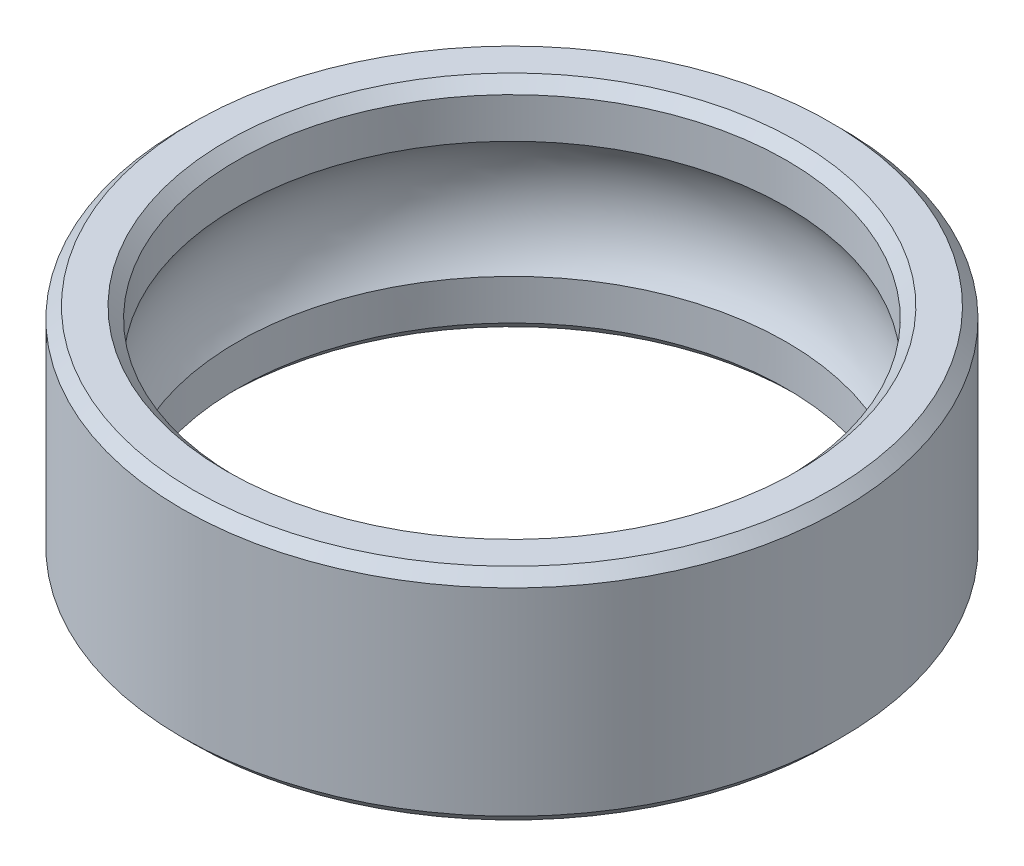
SolidWorks part; units mm, degrees
ref_plane "Front" through (0, 0, 0) normal (0, 0, 1) x (1, 0, 0)
ref_plane "Top" through (0, 0, 0) normal (0, 1, 0) x (1, 0, 0)
ref_plane "Right" through (0, 0, 0) normal (1, 0, 0) x (0, 0, -1)
sketch "Sketch1" plane through (0, 0, 0) normal (0, 1, 0) x (1, 0, 0)
  circle A0 centre (0, 0) radius 6
  circle A1 centre (0, 0) radius 5
extrude "Boss-Extrude1" add sketch "Sketch1" along normal mid plane 4
chamfer "Chamfer1" distance 0.2 angle 45 4 edges at (0, -2, 6) (0, -2, 5) (0, 2, 6) (0, 2, 5)
sketch "Sketch2" plane through (0, 0, 0) normal (1, 0, 0) x (0, 0, -1)
  circle A0 centre (-3.5491, 0) radius 1.8
sketch "Sketch3" plane through (0, 0, 0) normal (0, 1, 0) x (1, 0, 0)
  circle A0 centre (0, 0) radius 3.5422
sweep "Cut-Sweep1" cut profiles "Sketch2" path "Sketch3"
